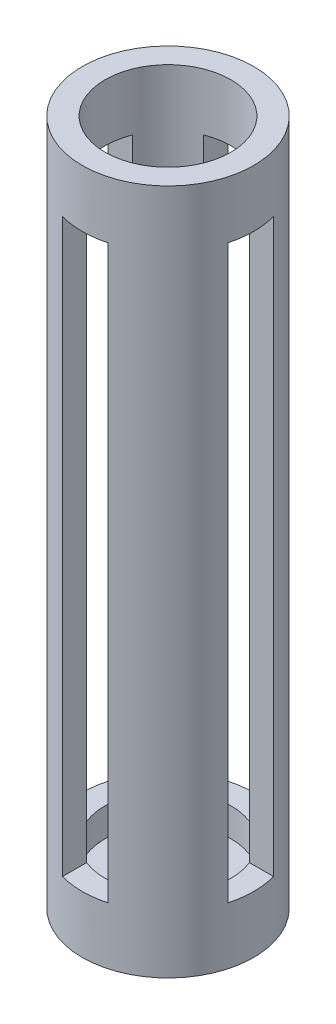
SolidWorks part; units mm, degrees
ref_plane "Front Plane" through (0, 0, 0) normal (0, 0, 1) x (1, 0, 0)
ref_plane "Top Plane" through (0, 0, 0) normal (0, 1, 0) x (1, 0, 0)
ref_plane "Right Plane" through (0, 0, 0) normal (1, 0, 0) x (0, 0, -1)
sketch "Sketch1" plane through (0, 0, 0) normal (0, 1, 0) x (1, 0, 0)
  circle A0 centre (0, 0) radius 13.97
  circle A1 centre (0, 0) radius 19.05
  dimension "D1" = 27.94
  dimension "D2" = 38.1
extrude "Boss-Extrude1" add sketch "Sketch1" along normal blind 152.4
sketch "Sketch2" plane through (0, 0, 0) normal (0, -1, 0) x (1, 0, 0)
  circle A0 centre (0, 0) radius 13.97
extrude "Boss-Extrude2" add sketch "Sketch2" against normal blind 6.35
ref_plane "Plane1" through (0, 0, 16.51) normal (0, 0, 1) x (1, 0, 0)
sketch "Sketch3" plane through (0, 0, 16.51) normal (0, 0, 1) x (1, 0, 0)
  line L0 (-19.05, 0) -> (19.05, 0) construction
  line L1 (0, 101.6) -> (0, 0) construction
  circle A0 centre (0, 101.6) radius 2.2479
  dimension "D1" = 4.4958
  dimension "D2" = 101.6
extrude "Cut-Extrude1" cut sketch "Sketch3" against normal through all and the other way through all contours A0
sketch "Sketch5" plane through (0, 0, 0) normal (1, 0, 0) x (0, 0, -1)
  line L0 (55, 0) -> (-55, 0) construction
  line L1 (5.08, 12.7) -> (-5.08, 12.7)
  line L2 (5.08, 12.7) -> (5.08, 139.7)
  line L3 (5.08, 139.7) -> (-5.08, 139.7)
  line L4 (-5.08, 12.7) -> (-5.08, 139.7)
  line L5 (19.05, 152.4) -> (-19.05, 152.4) construction
  line L6 (0, 0) -> (0, 12.7) construction
  line L7 (-5.08, 114.3) -> (7.62, 114.3)
  line L8 (-5.08, 88.9) -> (7.62, 88.9)
  line L9 (-5.08, 165.1) -> (5.08, 165.1)
  line L10 (-5.08, 190.5) -> (5.08, 190.5)
  dimension "D1" = 12.7
  dimension "D2" = 12.7
  dimension "D3" = 10.16
  dimension "D4" = 12.7
  dimension "D5" = 12.7
  dimension "D6" = 76.2
  dimension "D7" = 25.4
  dimension "D8" = 25.4
  dimension "D9" = 50.8
extrude "Cut-Extrude5" cut sketch "Sketch5" against normal through all both and the other way through all contours L8 L4 L1 L2 | L9 L4 L7 L2 | L4 L10 L2 L3
sketch "Sketch8" plane through (0, 0, 0) normal (0, 0, 1) x (1, 0, 0)
  line L0 (-19.05, 0) -> (19.05, 0) construction
  line L1 (5.08, 12.7) -> (-5.08, 12.7)
  line L2 (5.08, 12.7) -> (5.08, 139.7)
  line L3 (5.08, 139.7) -> (-5.08, 139.7)
  line L4 (-5.08, 12.7) -> (-5.08, 139.7)
  line L5 (19.05, 152.4) -> (-19.05, 152.4) construction
  line L6 (0, 12.7) -> (0, 0) construction
  line L7 (5.08, 88.9) -> (-5.08, 88.9)
  line L8 (5.08, 114.3) -> (-5.08, 114.3)
  line L9 (5.08, 165.1) -> (-5.08, 165.1)
  line L10 (5.08, 190.5) -> (-5.08, 190.5)
  dimension "D1" = 12.7
  dimension "D2" = 10.16
  dimension "D3" = 12.7
  dimension "D4" = 76.2
  dimension "D5" = 25.4
  dimension "D6" = 25.4
  dimension "D7" = 50.8
extrude "Cut-Extrude6" cut sketch "Sketch8" against normal through all both and the other way through all contours L2 L7 L4 L1 | L2 L9 L4 L8 | L10 L2 L3 L4
sketch "Sketch7" plane through (0, 6.35, 0) normal (0, 1, 0) x (1, 0, 0)
  circle A0 centre (0, 0) radius 6.35
extrude "Cut-Extrude4" cut sketch "Sketch7" against normal through all
sketch "Sketch9" plane through (0, 6.35, 0) normal (0, 1, 0) x (1, 0, 0)
  circle A1 centre (0, 0) radius 6.35 construction
  circle A2 centre (0, 0) radius 8.89
  circle A3 centre (0, 0) radius 8.89
  circle A4 centre (0, 0) radius 6.35
  dimension "D1" = 5.08
extrude "Boss-Extrude3" add sketch "Sketch9" along normal blind 19.05
sketch "Sketch10" plane through (0, 25.4, 0) normal (0, 1, 0) x (1, 0, 0)
  circle A0 centre (0, 0) radius 8.89 construction
  circle A1 centre (0, 0) radius 8.89
  circle A2 centre (0, 0) radius 5.08
  dimension "D1" = 3.81
extrude "Boss-Extrude4" add sketch "Sketch10" along normal blind 5.08
